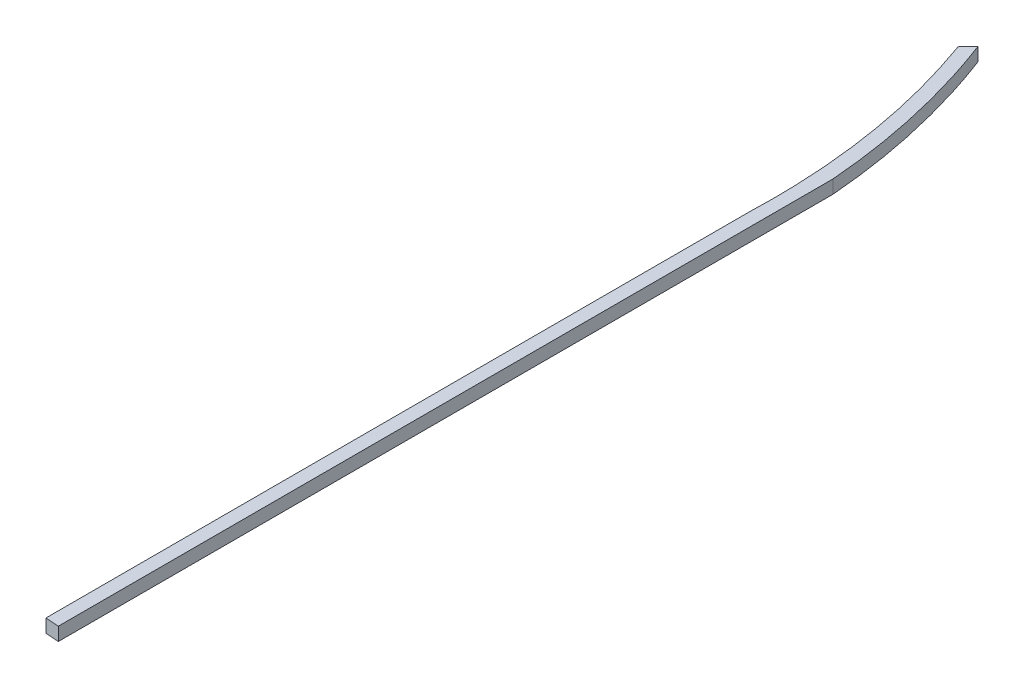
SolidWorks part; units mm, degrees
ref_plane "Front Plane" through (0, 0, 0) normal (0, 0, 1) x (1, 0, 0)
ref_plane "Top Plane" through (0, 0, 0) normal (0, 1, 0) x (1, 0, 0)
ref_plane "Right Plane" through (0, 0, 0) normal (1, 0, 0) x (0, 0, -1)
sketch "Sketch1" plane through (0, 0, 0) normal (0, 1, 0) x (1, 0, 0)
  line L0 (0, 0) -> (0, 301.474)
  line L2 (5.7, 331.474) -> (5.7, 0)
  line L3 (5.7, 0) -> (0, 0) construction
  line L8 (-16.5437, 407.3275) -> (-12.3882, 411.7104)
  line L9 (0, 0) -> (5.7, -0.4276)
  line L10 (5.7, -0.4276) -> (5.7, 0)
  spline S0 degree 2 poles (0, 301.474) (1.9472, 355.9346) (-16.5437, 407.3275) knots 0 0 0 1 1 1
  spline S1 degree 2 poles (5.7, 331.474) (2.4296, 372.72) (-12.3882, 411.7104) knots 0 0 0 1 1 1
  point P3 (-16.5437, 407.3275)
  point P8 (-12.3882, 411.7104)
  dimension "D1" = 301.474
  dimension "D2" = 5.7
  dimension "D3" = 4.29
extrude "Boss-Extrude1" add sketch "Sketch1" along normal blind 5.7
